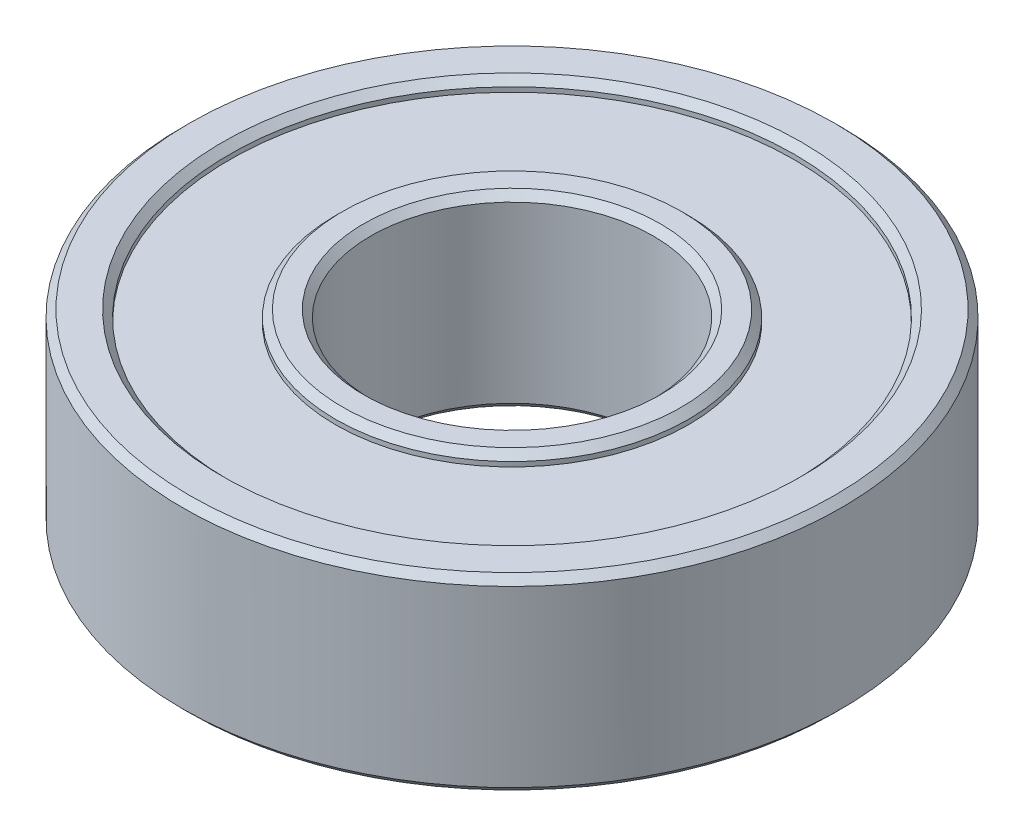
SolidWorks part; units mm, degrees
ref_plane "Front Plane" through (0, 0, 0) normal (0, 0, 1) x (1, 0, 0)
ref_plane "Top Plane" through (0, 0, 0) normal (0, 1, 0) x (1, 0, 0)
ref_plane "Right Plane" through (0, 0, 0) normal (1, 0, 0) x (0, 0, -1)
sketch "Sketch1" plane through (0, 0, 0) normal (0, 0, 1) x (1, 0, 0)
  line L0 (0, 0) -> (0, 8) construction
  line L1 (-6, 0) -> (-6, 8)
  line L2 (-6, 8) -> (-7.5, 8)
  line L3 (-7.5, 8) -> (-7.5, 7.5)
  line L4 (-7.5, 7.5) -> (-12, 7.5)
  line L5 (-12, 7.5) -> (-12, 8)
  line L6 (-12, 8) -> (-14, 8)
  line L7 (-14, 8) -> (-14, 0)
  line L8 (-14, 0) -> (-12, 0)
  line L9 (-12, 0) -> (-12, 0.5)
  line L10 (-12, 0.5) -> (-7.5, 0.5)
  line L11 (-7.5, 0.5) -> (-7.5, 0)
  line L12 (-7.5, 0) -> (-6, 0)
  dimension "D1" = 6
  dimension "D2" = 8
  dimension "D3" = 1.5
  dimension "D4" = 14
  dimension "D5" = 2
  dimension "D6" = 0.5
revolve "Revolve1" add sketch "Sketch1" angle 360 about L0
chamfer "Chamfer1" distance 0.3 angle 45 8 edges at (0, 0, -6) (0, 0, -7.5) (0, 0, -12) (0, 0, -14) (0, 8, -14) (0, 8, -6) (0, 8, -7.5) (0, 8, -12)
